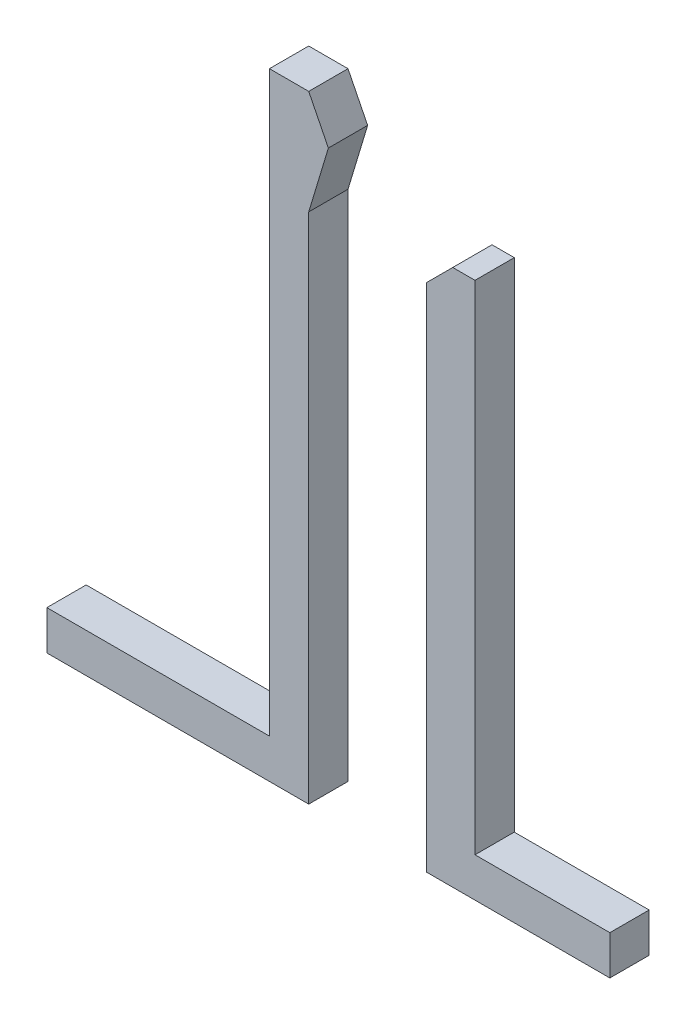
SolidWorks part; units mm, degrees
ref_plane "Plano frontal" through (0, 0, 0) normal (0, 0, 1) x (1, 0, 0)
ref_plane "Plano superior" through (0, 0, 0) normal (0, 1, 0) x (1, 0, 0)
ref_plane "Plano direito" through (0, 0, 0) normal (1, 0, 0) x (0, 0, -1)
sketch "Esboço1" plane through (0, 0, 0) normal (0, 0, 1) x (1, 0, 0)
  line L0 (-2.35, -0.1) -> (-0.35, -0.1)
  line L1 (-0.35, -0.1) -> (-0.35, 3.8174)
  line L2 (-0.35, 4.6148) -> (-0.65, 4.6148)
  line L3 (-0.65, 4.6148) -> (-0.65, 0.2)
  line L4 (-0.65, 0.2) -> (-2.35, 0.2)
  line L5 (-2.35, 0.2) -> (-2.35, -0.1)
  line L7 (-0.35, 4.6148) -> (-0.2, 4.3148)
  line L8 (-0.2, 4.3148) -> (-0.35, 3.8174)
  line L10 (1.95, -0.1) -> (0.55, -0.1)
  line L11 (0.55, -0.1) -> (0.55, 3.8)
  line L12 (0.75, 4) -> (0.92, 4)
  line L13 (0.92, 4) -> (0.92, 0.2)
  line L14 (0.92, 0.2) -> (1.95, 0.2)
  line L15 (1.95, 0.2) -> (1.95, -0.1)
  line L17 (0.55, 3.8) -> (0.75, 4)
  point P15 (0.55, 4)
  dimension "D1" = 2
  dimension "D3" = 1.7
  dimension "D4" = 0.15
  dimension "D5" = 0.3
  dimension "D6" = 0.3
  dimension "D10" = 1.4
extrude "Ressalto-extrusão1" add sketch "Esboço1" along normal blind 0.3
